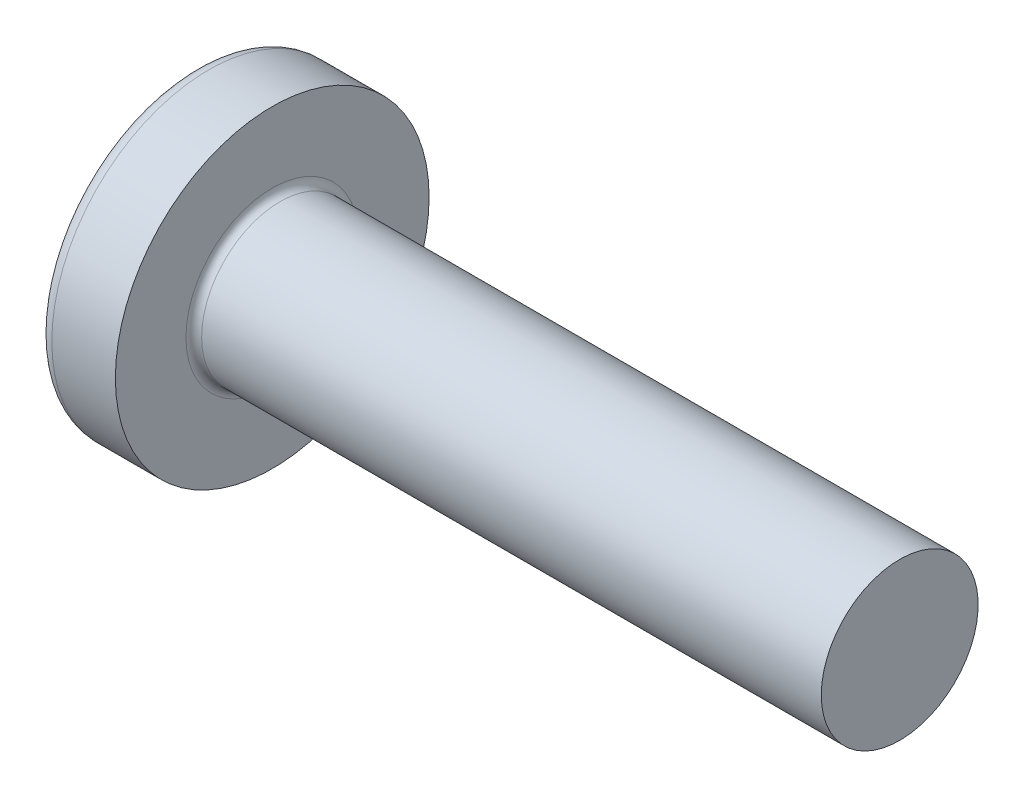
SolidWorks part; units mm, degrees
ref_plane "Plane1" through (0, 0, 0) normal (0, 0, 1) x (1, 0, 0)
ref_plane "Plane2" through (0, 0, 0) normal (0, 1, 0) x (1, 0, 0)
ref_plane "Plane3" through (0, 0, 0) normal (1, 0, 0) x (0, 0, -1)
sketch "BodySke" plane through (0, 0, 0) normal (0, 0, 1) x (1, 0, 0)
  line L0 (1.6, 1) -> (1.6, 2)
  line L1 (1.8, 6.35) -> (1.8, -3.175) construction
  line L2 (-25.4, 0) -> (127, 0) construction
  line L3 (9.6, 0) -> (0, 0)
  line L4 (1.6, 1) -> (9.6, 1)
  line L5 (9.6, 1) -> (9.6, 0)
  line L6 (0.79, 2) -> (1.6, 2)
  line L8 (1.6, 6.35) -> (1.6, -3.175) construction
  arc A0 (0.6464, 1.9285) -> (0, 0) centre (3.2, 0) ccw
  arc A2 (0.6464, 1.9285) -> (0.79, 2) centre (0.79, 1.82) cw
  dimension "Head_fillet_rad" = 0.18
  dimension "Head_crown_rad" = 3.2
  dimension "Head_ht" = 1.6
  dimension "Diameter" = 2
  dimension "Length" = 8
  dimension "Head_dia" = 4
  dimension "Advance" = 0.4
  dimension "Thread_nom" = 8
revolve "Base-Revolve" add sketch "BodySke"
cosmetic thread "ThreadCosmetic" [suppressed]
fillet "Fillet1" radius 0.1 1 edges at (1.6, 0, 1)
sketch "Sketch3" plane through (0, 0, 0) normal (1, 0, 0) x (0, 0, -1)
  line L0 (0.24, -1.05) -> (-0.24, -1.05)
  line L1 (0.24, -1.05) -> (0.24, 1.05)
  line L2 (-0.24, 1.05) -> (0.24, 1.05)
  line L3 (-0.24, 1.05) -> (-0.24, -1.05)
  dimension "D1" = 1.05
  dimension "Cross_dia" = 2.1
  dimension "D2" = 0.24
  dimension "Cross_width" = 0.48
ref_plane "Plane4" through (1.42, 0, 0) normal (1, 0, 0) x (0, 0, -1)
sketch "Sketch4" plane through (1.42, 0, 0) normal (1, 0, 0) x (0, 0, -1)
  line L0 (0.24, -0.342) -> (-0.24, -0.342)
  line L1 (0.24, -0.342) -> (0.24, 0.342)
  line L2 (-0.24, 0.342) -> (0.24, 0.342)
  line L3 (-0.24, 0.342) -> (-0.24, -0.342)
  dimension "D1" = 0.48
  dimension "D2" = 0.684
  dimension "D3" = 0.24
  dimension "D4" = 0.342
loft "Recess" cut profiles "Sketch3", "Sketch4"
pattern_circular "RecPat" count 2 every 90 about axis through (0, 0, 0) along (1, 0, 0) of "Recess"
sketch "RecCorSke" plane through (0, 0, 0) normal (0, 0, 1) x (1, 0, 0)
  line L0 (-3.175, 0) -> (15.875, 0) construction
  line L1 (-25.4, 0) -> (127, 0) construction
  line L2 (0, 0) -> (0, 0.4548)
  line L3 (0, 0.4548) -> (1.42, 0.3555)
  line L4 (1.42, 0.3555) -> (1.5355, 0)
  line L5 (1.5355, 0) -> (0, 0)
  dimension "Diameter" = 0.711
  dimension "Depth" = 1.42
  dimension "Draft_angle" = 4
  dimension "Bottom_angle" = 18
revolve "RecessCore" cut sketch "RecCorSke" angle 360 about L0
sketch "ThdSchSke" plane through (0, 0, 0) normal (0, 0, 1) x (1, 0, 0)
  line L0 (2.4, -0.774) -> (2.2418, -1)
  line L1 (2.4, -0.774) -> (2.5582, -1)
  line L2 (2.5582, -1) -> (2.5582, -1.25)
  line L3 (-3.175, 0) -> (5.1513, 0) construction
  line L5 (2.5582, -1.25) -> (2.2418, -1.25)
  line L6 (2.2418, -1.25) -> (2.2418, -1)
  dimension "Thread_minor" = 1.548
  dimension "Diameter" = 2
  dimension "Start" = 2.4
  dimension "SideAngle" = 55
  dimension "VeeAngle" = 70
  dimension "Overcut" = 2.5
revolve "ThreadSchematic" [suppressed] cut sketch "ThdSchSke" angle 360 about L3
pattern_linear "ThdSchPat" [suppressed]
equation "\"D1@Sketch3\" = \"Cross_dia@Sketch3\" / 2"
equation "\"D2@Sketch3\" = \"Cross_width@Sketch3\" / 2"
equation "\"Depth@RecCorSke\" = \"Cross_depth@Plane4\""
equation "\"D1@Sketch4\" = \"Cross_width@Sketch3\""
equation "\"D2@Sketch4\" = \"Cross_dia@Sketch3\" - 2.0 * \"Cross_depth@Plane4\" * tan(26.5  * 0.017453292)"
equation "\"D3@Sketch4\" = \"D1@Sketch4\" / 2"
equation "\"D4@Sketch4\" = \"D2@Sketch4\" / 2"
equation "\"Thread_length@ThreadCosmetic\" = ((sgn( (\"Length@BodySke\" - \"Advance@BodySke\" * 2.0 ) - \"Thread_nom@BodySke\" )-1)*( (\"Length@BodySke\" - \"Advance@BodySke\" * 2.0 ) - \"Thread_nom@BodySke\" ))/-2+ \"Thread_nom@BodySke\""
equation "\"Thread_minor@ThdSchSke\" = \"Thread_minor@ThreadCosmetic\""
equation "\"Diameter@ThdSchSke\" = \"Diameter@BodySke\""
equation "\"Overcut@ThdSchSke\" = \"Diameter@BodySke\" * 1.25"
equation "\"Start@ThdSchSke\" = \"Head_ht@BodySke\" + \"Length@BodySke\" - \"Thread_length@ThreadCosmetic\"  '---Non-countersunk---"
equation "\"Num_threads@ThdSchPat\" = int( \"Thread_length@ThreadCosmetic\" / \"Advance@BodySke\" + 0.999 )  + 1"
equation "\"Advance@ThdSchPat\" = \"Thread_length@ThreadCosmetic\" /  (\"Num_threads@ThdSchPat\" - 1) 'relax it"
